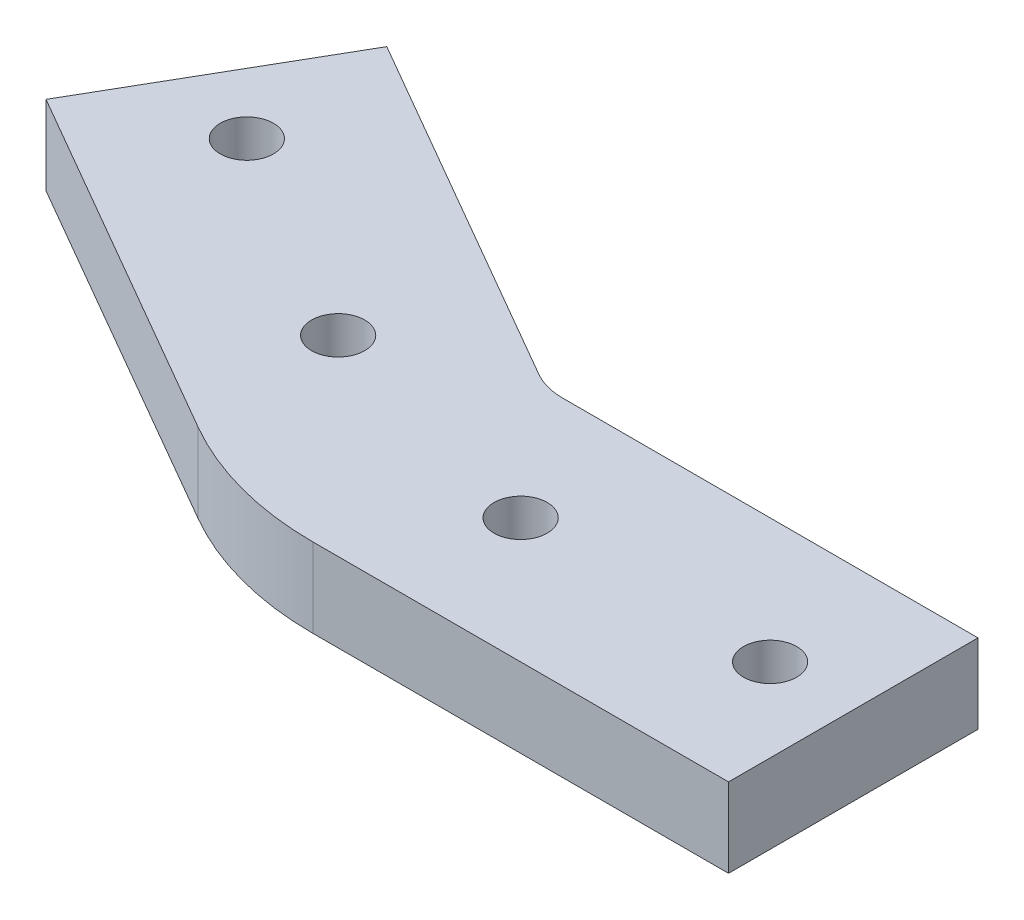
SolidWorks part; units mm, degrees
ref_plane "Front Plane" through (0, 0, 0) normal (0, 0, 1) x (1, 0, 0)
ref_plane "Top Plane" through (0, 0, 0) normal (0, 1, 0) x (1, 0, 0)
ref_plane "Right Plane" through (0, 0, 0) normal (1, 0, 0) x (0, 0, -1)
sketch "Sketch1" plane through (0, 0, 0) normal (0, 1, 0) x (1, 0, 0)
  line L0 (0, 0) -> (28.0331, 0) construction
  line L1 (0, 0) -> (-24.2774, 14.0166) construction
  line L2 (28.0331, 7.5) -> (28.0331, -7.5)
  line L3 (28.0331, -7.5) -> (3.0331, -7.5)
  line L4 (-6.3767, -4.9786) -> (-28.0274, 7.5214)
  line L5 (-28.0274, 7.5214) -> (-20.5274, 20.5117)
  line L6 (-20.5274, 20.5117) -> (1.1233, 8.0117)
  line L7 (3.0331, 7.5) -> (28.0331, 7.5)
  arc A0 (3.0331, -7.5) -> (-6.3767, -4.9786) centre (3.0331, 11.3197) cw
  arc A1 (1.1233, 8.0117) -> (3.0331, 7.5) centre (3.0331, 11.3197) ccw
  circle A2 centre (23.0331, 0) radius 1.6
  circle A3 centre (8.0331, 0) radius 1.6
  circle A4 centre (-19.9473, 11.5166) radius 1.6
  circle A5 centre (-6.9569, 4.0166) radius 1.6
  dimension "D3" = 2
  dimension "D1" = 3.2
  dimension "angle" = 150
  dimension "D2" = 15
  dimension "D4" = 25
  dimension "D5" = 5
  dimension "D6" = 15
  dimension "D7" = 5
  dimension "D8" = 15
extrude "Boss-Extrude1" add sketch "Sketch1" along normal blind 4.7625
